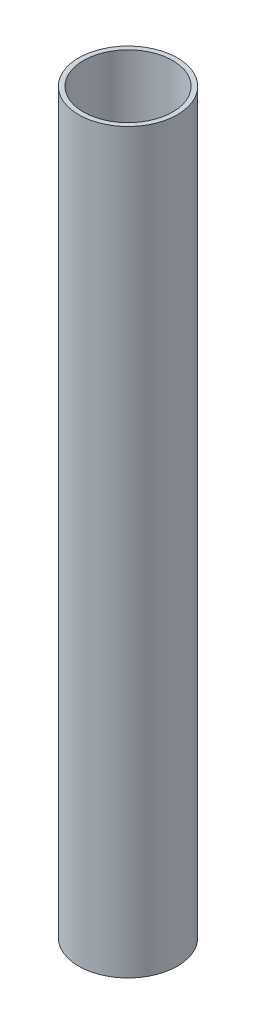
SolidWorks part; units mm, degrees
ref_plane "Front Plane" through (0, 0, 0) normal (0, 0, 1) x (1, 0, 0)
ref_plane "Top Plane" through (0, 0, 0) normal (0, 1, 0) x (1, 0, 0)
ref_plane "Right Plane" through (0, 0, 0) normal (1, 0, 0) x (0, 0, -1)
sketch "Sketch1" plane through (0, 0, 0) normal (0, 1, 0) x (1, 0, 0)
  circle A0 centre (0, 0) radius 21
sketch "Sketch2" plane through (0, 0, 0) normal (0, 1, 0) x (1, 0, 0)
  circle A0 centre (0, 0) radius 19
extrude "Extrude-Thin2" add sketch "Sketch2" along normal blind 314 thin
